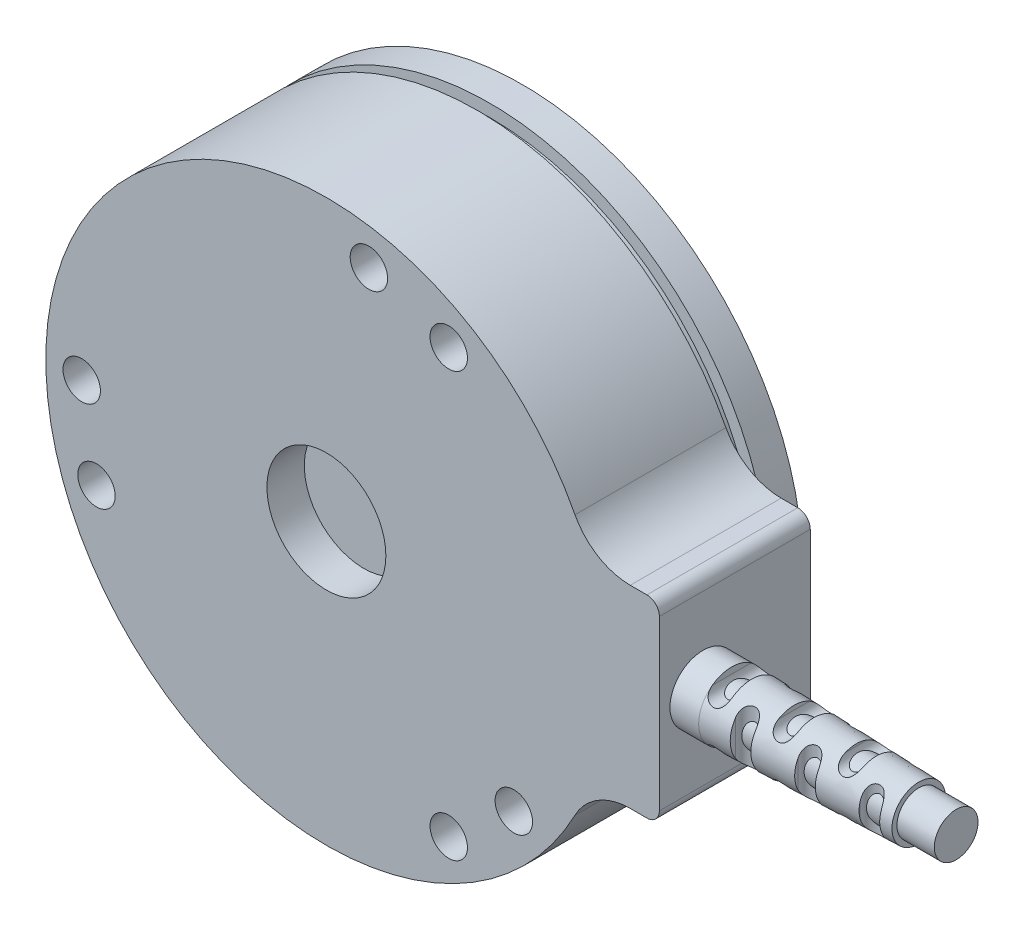
SolidWorks part; units mm, degrees
ref_plane "Piano frontale" through (0, 0, 0) normal (0, 0, 1) x (1, 0, 0)
ref_plane "Piano superiore" through (0, 0, 0) normal (0, 1, 0) x (1, 0, 0)
ref_plane "Piano destro" through (0, 0, 0) normal (1, 0, 0) x (0, 0, -1)
sketch "Schizzo1" plane through (0, 0, 0) normal (0, 0, 1) x (1, 0, 0)
  line L0 (0, 33.4226) -> (0, -33.5599) construction
  line L1 (-26.436, 0) -> (79.836, 0) construction
  line L2 (26.7, 6.75) -> (26.7, -6.75)
  line L3 (25.7, 7.75) -> (24.3657, 7.75)
  line L4 (25.7, -7.75) -> (24.3657, -7.75)
  line L5 (-39.3333, 14.3161) -> (50.0827, -18.2286) construction
  line L6 (12.1645, 33.4218) -> (-12.2682, -33.7066) construction
  line L7 (0, 0) -> (9.81, 16.9914) construction
  arc A0 (19.9356, 10.4318) -> (19.9356, -10.4318) centre (0, 0) ccw
  arc A1 (26.7, 6.75) -> (25.7, 7.75) centre (25.7, 6.75) ccw
  arc A2 (26.7, -6.75) -> (25.7, -7.75) centre (25.7, -6.75) cw
  arc A3 (24.3657, -7.75) -> (19.9356, -10.4318) centre (24.3657, -12.75) ccw
  arc A4 (24.3657, 7.75) -> (19.9356, 10.4318) centre (24.3657, 12.75) cw
  circle A5 centre (0, 0) radius 19.62 construction
  circle A6 centre (9.81, 16.9914) radius 1.5
  circle A7 centre (3.407, 19.3219) radius 1.5
  circle A8 centre (15.0298, -12.6115) radius 1.5
  circle A9 centre (9.81, -16.9914) radius 1.5
  circle A10 centre (-18.4368, -6.7104) radius 1.5
  circle A11 centre (-19.62, 0) radius 1.5
  point P9 (26.7, 0)
  point P13 (26.7, 7.75)
  point P16 (26.7, -7.75)
  point P41 (0, 0)
  dimension "D1" = 45
  dimension "D4" = 1
  dimension "D5" = 5
  dimension "D7" = 39.24
  dimension "D8" = 3
  dimension "D2" = 15.5
  dimension "D3" = 26.7
  dimension "D6" = 20
  dimension "D9" = 10
  dimension "D10" = 3
extrude "Estrusione-Estrusione1" add sketch "Schizzo1" along normal blind 5
sketch "Schizzo2" plane through (0, 0, 5) normal (0, 0, 1) x (1, 0, 0)
  circle A0 centre (0, 0) radius 4.769
  dimension "D1" = 9.538
extrude "Taglio-Estrusione1" cut sketch "Schizzo2" against normal blind 3
sketch "Schizzo3" plane through (0, 0, 0) normal (0, 0, -1) x (-1, 0, 0)
  line L3 (-26.7, 6.75) -> (-26.7, -6.75)
  line L4 (-25.7, -7.75) -> (-24.3657, -7.75)
  line L5 (-24.3657, 7.75) -> (-25.7, 7.75)
  line L6 (-26.7, 6.75) -> (-26.7, -6.75)
  line L7 (-25.7, -7.75) -> (-24.3657, -7.75)
  line L8 (-24.3657, 7.75) -> (-25.7, 7.75)
  arc A5 (-25.7, 7.75) -> (-26.7, 6.75) centre (-25.7, 6.75) ccw
  arc A6 (-26.7, -6.75) -> (-25.7, -7.75) centre (-25.7, -6.75) ccw
  arc A7 (-19.9356, -10.4318) -> (-24.3657, -7.75) centre (-24.3657, -12.75) ccw
  arc A8 (-19.9356, -10.4318) -> (-19.9356, 10.4318) centre (0, 0) ccw
  arc A9 (-24.3657, 7.75) -> (-19.9356, 10.4318) centre (-24.3657, 12.75) ccw
  arc A10 (-25.7, 7.75) -> (-26.7, 6.75) centre (-25.7, 6.75) ccw
  arc A11 (-26.7, -6.75) -> (-25.7, -7.75) centre (-25.7, -6.75) ccw
  arc A12 (-19.9356, -10.4318) -> (-24.3657, -7.75) centre (-24.3657, -12.75) ccw
  arc A13 (-19.9356, -10.4318) -> (-19.9356, 10.4318) centre (0, 0) ccw
  arc A14 (-24.3657, 7.75) -> (-19.9356, 10.4318) centre (-24.3657, 12.75) ccw
  dimension "D1" = 0
extrude "Estrusione-Estrusione2" add sketch "Schizzo3" along normal blind 7.1
sketch "Schizzo4" plane through (0, 0, -7.1) normal (0, 0, -1) x (-1, 0, 0)
  circle A0 centre (0, 0) radius 21.5
  dimension "D1" = 43
extrude "Estrusione-Estrusione3" add sketch "Schizzo4" along normal blind 1 contours A0
sketch "Schizzo5" plane through (0, 0, -8.1) normal (0, 0, -1) x (-1, 0, 0)
  circle A0 centre (0, 0) radius 22.5
  dimension "D1" = 45
extrude "Estrusione-Estrusione4" add sketch "Schizzo5" along normal blind 2.6
sketch "Schizzo6" plane through (26.7, 0, 0) normal (1, 0, 0) x (0, 0, -1)
  line L0 (-5, -6.75) -> (-5, 6.75) construction
  circle A0 centre (-1.5, 0) radius 2.65
  dimension "D1" = 5.3
  dimension "D2" = 3.5
extrude "Estrusione-Estrusione5" add sketch "Schizzo6" along normal blind 17.3
chamfer "Smusso1" distance 15 distance2 0.5 1 edges at (44, 0, -1.15)
sketch "Schizzo7" plane through (0, 0, 5) normal (0, 0, 1) x (1, 0, 0)
  line L0 (26.7, 0) -> (44, 0) construction
  line L1 (26.7, -6.75) -> (26.7, 6.75) construction
  line L2 (44, -2.15) -> (44, 2.15) construction
  line L3 (29, 2.65) -> (44, 2.65) construction
  line L5 (29.8, 2.15) -> (29.8, 3.15) construction
  line L6 (29, 2.15) -> (29, 3.15)
  line L7 (30.6, 2.15) -> (30.6, 3.15)
  line L8 (29, -2.65) -> (29, 2.65) construction
  line L9 (34.8, 2.15) -> (34.8, 3.15) construction
  line L10 (34, 2.15) -> (34, 3.15)
  line L11 (35.6, 2.15) -> (35.6, 3.15)
  line L12 (39.8, 2.15) -> (39.8, 3.15) construction
  line L13 (39, 2.15) -> (39, 3.15)
  line L14 (40.6, 2.15) -> (40.6, 3.15)
  line L15 (29, -2.65) -> (44, -2.65) construction
  line L16 (39.8, -2.15) -> (39.8, -3.15) construction
  line L17 (39, -2.15) -> (39, -3.15)
  line L18 (40.6, -2.15) -> (40.6, -3.15)
  line L19 (34.8, -2.15) -> (34.8, -3.15) construction
  line L20 (34, -2.15) -> (34, -3.15)
  line L21 (35.6, -2.15) -> (35.6, -3.15)
  line L22 (29.8, -2.15) -> (29.8, -3.15) construction
  line L23 (29, -2.15) -> (29, -3.15)
  line L24 (30.6, -2.15) -> (30.6, -3.15)
  arc A0 (29, 2.15) -> (30.6, 2.15) centre (29.8, 2.15) ccw
  arc A1 (30.6, 3.15) -> (29, 3.15) centre (29.8, 3.15) ccw
  arc A2 (34, 2.15) -> (35.6, 2.15) centre (34.8, 2.15) ccw
  arc A3 (35.6, 3.15) -> (34, 3.15) centre (34.8, 3.15) ccw
  arc A4 (39, 2.15) -> (40.6, 2.15) centre (39.8, 2.15) ccw
  arc A5 (40.6, 3.15) -> (39, 3.15) centre (39.8, 3.15) ccw
  arc A6 (39, -2.15) -> (40.6, -2.15) centre (39.8, -2.15) cw
  arc A7 (40.6, -3.15) -> (39, -3.15) centre (39.8, -3.15) cw
  arc A8 (34, -2.15) -> (35.6, -2.15) centre (34.8, -2.15) cw
  arc A9 (35.6, -3.15) -> (34, -3.15) centre (34.8, -3.15) cw
  arc A10 (29, -2.15) -> (30.6, -2.15) centre (29.8, -2.15) cw
  arc A11 (30.6, -3.15) -> (29, -3.15) centre (29.8, -3.15) cw
  point P10 (29.8, 2.65)
  point P16 (29.8, 3.95)
  point P22 (34.8, 2.65)
  point P29 (39.8, 2.65)
  point P37 (39.8, -2.65)
  point P44 (34.8, -2.65)
  point P51 (29.8, -2.65)
  dimension "D1" = 0.8
  dimension "D2" = 1
  dimension "D3" = 3
extrude "Taglio-Estrusione2" cut sketch "Schizzo7" against normal through all
sketch "Schizzo8" plane through (0, 7.75, 0) normal (0, 1, 0) x (1, 0, 0)
  line L0 (29, -1.5) -> (44, -1.5) construction
  line L1 (29, -3.0492) -> (29, 0.0492) construction
  line L2 (44, -3.65) -> (44, 0.65) construction
  line L3 (29, 1.15) -> (44, 1.15) construction
  line L4 (32.25, 0.65) -> (32.25, 1.65) construction
  line L5 (31.45, 0.65) -> (31.45, 1.65)
  line L6 (33.05, 0.65) -> (33.05, 1.65)
  line L7 (29, 1.15) -> (29, 0.0492) construction
  line L8 (37.25, 0.65) -> (37.25, 1.65) construction
  line L9 (36.45, 0.65) -> (36.45, 1.65)
  line L10 (38.05, 0.65) -> (38.05, 1.65)
  line L11 (42.25, 0.65) -> (42.25, 1.65) construction
  line L12 (41.45, 0.65) -> (41.45, 1.65)
  line L13 (43.05, 0.65) -> (43.05, 1.65)
  line L14 (42.25, -3.65) -> (42.25, -4.65) construction
  line L15 (41.45, -3.65) -> (41.45, -4.65)
  line L16 (43.05, -3.65) -> (43.05, -4.65)
  line L17 (37.25, -3.65) -> (37.25, -4.65) construction
  line L18 (36.45, -3.65) -> (36.45, -4.65)
  line L19 (38.05, -3.65) -> (38.05, -4.65)
  line L20 (32.25, -3.65) -> (32.25, -4.65) construction
  line L21 (31.45, -3.65) -> (31.45, -4.65)
  line L22 (33.05, -3.65) -> (33.05, -4.65)
  arc A0 (31.45, 0.65) -> (33.05, 0.65) centre (32.25, 0.65) ccw
  arc A1 (33.05, 1.65) -> (31.45, 1.65) centre (32.25, 1.65) ccw
  arc A2 (36.45, 0.65) -> (38.05, 0.65) centre (37.25, 0.65) ccw
  arc A3 (38.05, 1.65) -> (36.45, 1.65) centre (37.25, 1.65) ccw
  arc A4 (41.45, 0.65) -> (43.05, 0.65) centre (42.25, 0.65) ccw
  arc A5 (43.05, 1.65) -> (41.45, 1.65) centre (42.25, 1.65) ccw
  arc A6 (41.45, -3.65) -> (43.05, -3.65) centre (42.25, -3.65) cw
  arc A7 (43.05, -4.65) -> (41.45, -4.65) centre (42.25, -4.65) cw
  arc A8 (36.45, -3.65) -> (38.05, -3.65) centre (37.25, -3.65) cw
  arc A9 (38.05, -4.65) -> (36.45, -4.65) centre (37.25, -4.65) cw
  arc A10 (31.45, -3.65) -> (33.05, -3.65) centre (32.25, -3.65) cw
  arc A11 (33.05, -4.65) -> (31.45, -4.65) centre (32.25, -4.65) cw
  point P11 (32.25, 1.15)
  point P21 (37.25, 1.15)
  point P28 (42.25, 1.15)
  point P34 (42.25, -4.15)
  point P41 (37.25, -4.15)
  point P48 (32.25, -4.15)
  dimension "D2" = 0.8
  dimension "D1" = 1
  dimension "D3" = 3.25
  dimension "D4" = 3
extrude "Taglio-Estrusione3" cut sketch "Schizzo8" against normal through all
sketch "Schizzo9" plane through (44, 0, 0) normal (1, 0, 0) x (0, 0, -1)
  circle A0 centre (-1.5, 0) radius 1.75
  dimension "D1" = 3.5
extrude "Estrusione-Estrusione6" add sketch "Schizzo9" along normal blind 3 and the other way blind 17.3
sketch "Schizzo10" plane through (0, 0, -10.7) normal (0, 0, -1) x (-1, 0, 0)
  line L0 (0, 0) -> (-59.7579, 0) construction
  line L1 (-57.3086, 20.8586) -> (57.3086, -20.8586) construction
  line L2 (14.6805, 40.3343) -> (-14.6805, -40.3343) construction
  line L3 (13.8858, -2.4484) -> (0, 0) construction
  line L4 (12.211, 7.05) -> (0, 0) construction
  circle A0 centre (0, 0) radius 14.1 construction
  circle A1 centre (13.8858, -2.4484) radius 1.5
  circle A2 centre (12.211, 7.05) radius 1.5
  circle A3 centre (0, -14.1) radius 1.5
  circle A4 centre (-9.0633, -10.8012) radius 1.5
  circle A5 centre (-12.211, 7.05) radius 1.5
  circle A6 centre (-4.8225, 13.2497) radius 1.5
  circle A7 centre (0, 0) radius 4.788
  point P22 (0, 0)
  dimension "D2" = 28.2
  dimension "D3" = 3
  dimension "D4" = 3
  dimension "D8" = 9.576
  dimension "D1" = 20
  dimension "D5" = 10
  dimension "D6" = 40
  dimension "D7" = 3
extrude "Taglio-Estrusione4" cut sketch "Schizzo10" against normal blind 3
